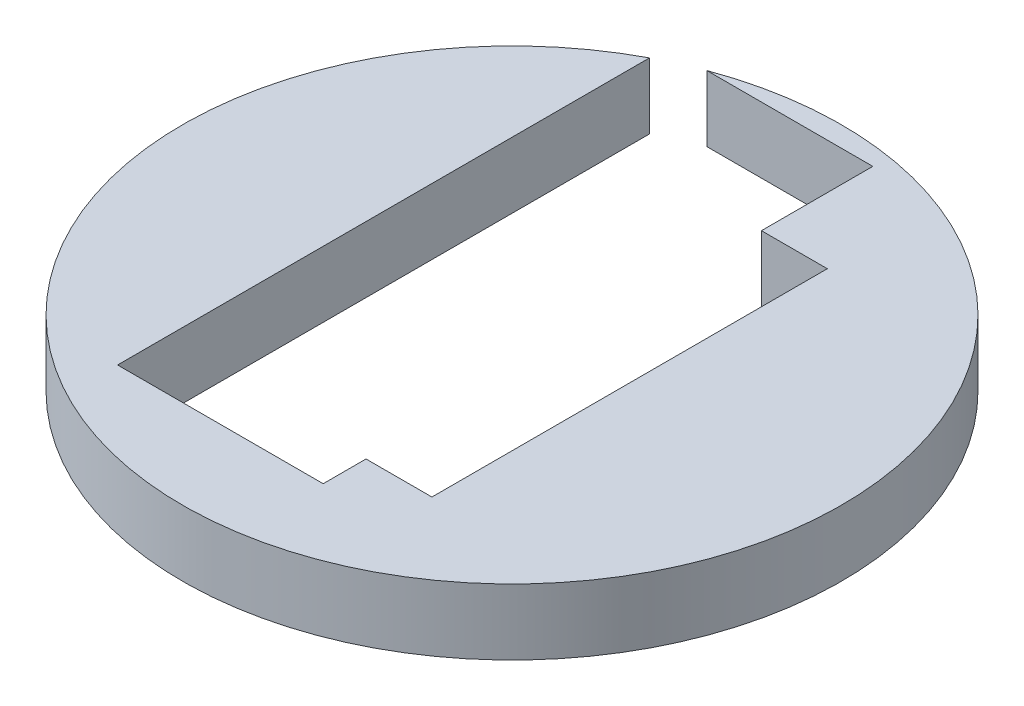
SolidWorks part; units mm, degrees
material "Polylactic Acid (PLA)"
ref_plane "Front Plane" through (0, 0, 0) normal (0, 0, 1) x (1, 0, 0)
ref_plane "Top Plane" through (0, 0, 0) normal (0, 1, 0) x (1, 0, 0)
ref_plane "Right Plane" through (0, 0, 0) normal (1, 0, 0) x (0, 0, -1)
sketch "Sketch1" plane through (0, 0, 0) normal (0, 1, 0) x (1, 0, 0)
  circle A0 centre (0, 0) radius 47.625
  dimension "D1" = 95.25
extrude "Boss-Extrude1" add sketch "Sketch1" against normal blind 12.7
sketch "Sketch2" plane through (0, 0, 0) normal (0, 1, 0) x (1, 0, 0)
  line L0 (0, -50.8) -> (0, 44.45) construction
  line L11 (26.035, 5.08) -> (26.035, -36.0275)
  line L12 (-30.48, 5.08) -> (-26.035, 5.08)
  line L14 (19.685, 25.0825) -> (15.24, 25.0825)
  line L15 (15.24, 25.0825) -> (15.24, 41.7558)
  line L16 (-30.48, 5.08) -> (-30.48, -32.3539)
  line L18 (-19.685, 25.0825) -> (-19.685, 39.8535)
  line L19 (19.685, 25.0825) -> (19.685, 39.8535)
  line L20 (-15.24, 25.0825) -> (-15.24, 41.7558)
  line L21 (-19.685, 25.0825) -> (-15.24, 25.0825)
  line L22 (-26.035, 5.08) -> (-26.035, -36.0275)
  line L23 (30.48, 5.08) -> (30.48, -32.3539)
  line L27 (30.48, 5.08) -> (26.035, 5.08)
  circle A2 centre (0, 0) radius 47.625
  circle A6 centre (0, 0) radius 44.45
  dimension "D1" = 88.9
  dimension "D8" = 95.25
  dimension "D2" = 6.35
  dimension "D3" = 4.445
  dimension "D4" = 4.445
  dimension "D5" = 26.035
  dimension "D6" = 5.08
  dimension "D7" = 20.0025
extrude "Boss-Extrude4" add sketch "Sketch2" along normal blind 12.7 separate body
sketch "Sketch10" plane through (0, 0, 0) normal (0, 1, 0) x (1, 0, 0)
  line L0 (3.81, 44.2864) -> (3.81, -44.2864) construction
  line L2 (10.16, -43.2733) -> (10.16, 43.2733)
  line L3 (4.7625, -44.1941) -> (4.7625, 44.1941)
  arc A1 (10.16, 43.2733) -> (3.81, 44.2864) centre (0, 0) ccw
  arc A2 (3.81, -44.2864) -> (10.16, -43.2733) centre (0, 0) ccw
  dimension "D2" = 3.81
  dimension "D1" = 88.9
  dimension "D3" = 6.35
  dimension "D4" = 0.9525
extrude "Boss-Extrude5" add sketch "Sketch10" along normal blind 4.7625 separate body
sketch "Sketch13" plane through (0, 0, 0) normal (0, 1, 0) x (1, 0, 0)
  line L0 (3.81, -59.065) -> (3.81, 65.3266) construction
  circle A2 centre (-4.9213, 13.5255) radius 8.7312 construction
  circle A3 centre (-4.9213, 13.5255) radius 9.525 construction
  dimension "D2" = 17.4625
  dimension "D3" = 19.05
  dimension "D1" = 3.81
  dimension "D4" = 8.4455
sketch "Sketch14" plane through (0, -12.7, 0) normal (0, -1, 0) x (1, 0, 0)
  line L0 (4.9847, -13.5255) -> (-14.8272, -13.5255) construction
  line L2 (4.9848, -29.7815) -> (-14.8272, -29.7815)
  line L3 (4.9848, -29.7815) -> (4.9847, 23.1775)
  line L4 (4.9847, 23.1775) -> (-14.8272, 23.1775)
  line L5 (-14.8272, -29.7815) -> (-14.8272, 23.1775)
  point P4 (-4.9213, -13.5255)
  dimension "D1" = 52.959
  dimension "D2" = 19.812
  dimension "D3" = 16.256
extrude "Cut-Extrude11" cut sketch "Sketch14" against normal blind 9.2758
sketch "Sketch18" plane through (0, -12.7, 0) normal (0, -1, 0) x (1, 0, 0)
  line L0 (-31.75, 0) -> (31.75, 0) construction
  line L1 (-14.8272, 23.1775) -> (4.9848, 23.1775)
  line L2 (-14.8272, 23.1775) -> (-14.8272, -28.0752)
  line L3 (-11.0057, -29.7815) -> (4.9848, -29.7815)
  line L4 (4.9848, 23.1775) -> (4.9847, 19.05)
  line L5 (4.9848, -19.05) -> (4.9848, -29.7815)
  line L6 (4.9847, 19.05) -> (11.3347, 19.05)
  line L8 (4.9848, -19.05) -> (11.3348, -19.05)
  line L9 (11.3347, 19.05) -> (11.3348, -19.05)
  arc A0 (-11.0057, -29.7815) -> (-14.8272, -28.0752) centre (0, 0) ccw
  dimension "D1" = 6.35
  dimension "D2" = 38.1
  dimension "D3" = 19.05
extrude "Boss-Extrude7" add sketch "Sketch18" along normal blind 6.35 separate body
delete or keep bodies "Body-Delete/Keep 1" type delete bodies bodies 124 118 122
